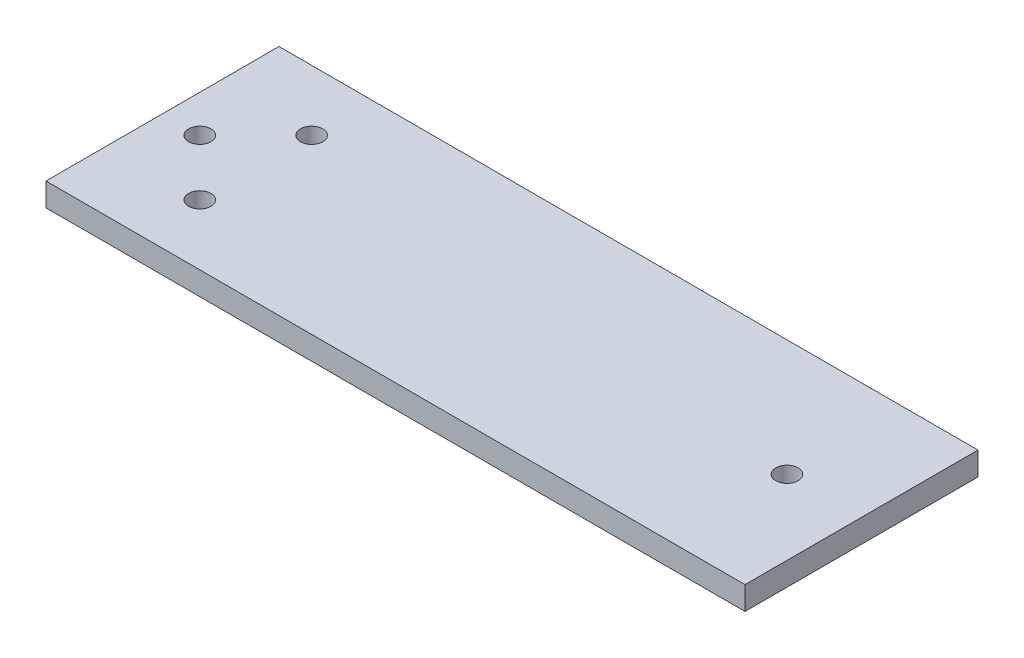
SolidWorks part; units mm, degrees
ref_plane "Front Plane" through (0, 0, 0) normal (0, 0, 1) x (1, 0, 0)
ref_plane "Top Plane" through (0, 0, 0) normal (0, 1, 0) x (1, 0, 0)
ref_plane "Right Plane" through (0, 0, 0) normal (1, 0, 0) x (0, 0, -1)
sketch "Sketch1" plane through (0, 0, 0) normal (0, 1, 0) x (1, 0, 0)
  line L1 (-37.5, -12.5) -> (37.5, -12.5)
  line L2 (-37.5, -12.5) -> (-37.5, 12.5)
  line L3 (-37.5, 12.5) -> (37.5, 12.5)
  line L4 (37.5, -12.5) -> (37.5, 12.5)
  line L5 (-37.5, -12.5) -> (37.5, 12.5) construction
  line L6 (-37.5, 12.5) -> (37.5, -12.5) construction
  point P0 (0, 0)
  dimension "D1" = 75
  dimension "D2" = 25
extrude "Boss-Extrude1" add sketch "Sketch1" along normal blind 2.5
sketch "Sketch2" plane through (0, 2.5, 0) normal (0, 1, 0) x (1, 0, 0)
  line L0 (-37.5, 0) -> (37.5, 0) construction
  line L1 (-37.5, 12.5) -> (-37.5, -12.5) construction
  line L2 (37.5, -12.5) -> (37.5, 12.5) construction
  circle A0 centre (-33.5, 0) radius 1.2
  circle A1 centre (-27.5, 6) radius 1.2
  circle A2 centre (-27.5, -6) radius 1.2
  circle A3 centre (29.5, 0) radius 1.2
  dimension "D1" = 2.4
  dimension "D2" = 8
  dimension "D3" = 6
  dimension "D4" = 6
  dimension "D5" = 4
  dimension "D6" = 6
extrude "Cut-Extrude1" cut sketch "Sketch2" against normal through all
